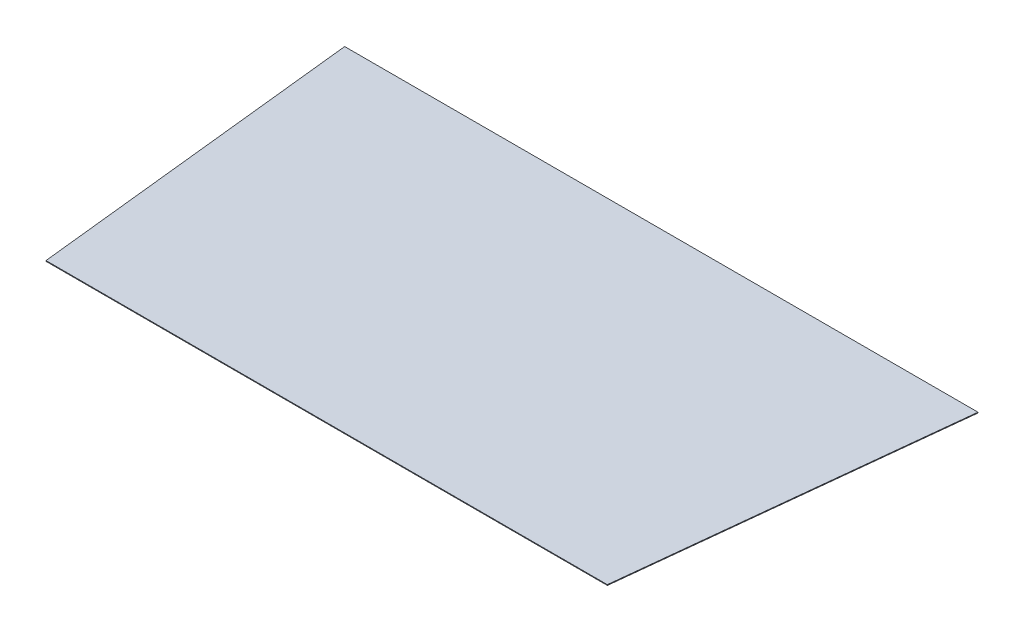
SolidWorks part; units mm, degrees
ref_plane "Front Plane" through (0, 0, 0) normal (0, 0, 1) x (1, 0, 0)
ref_plane "Top Plane" through (0, 0, 0) normal (0, 1, 0) x (1, 0, 0)
ref_plane "Right Plane" through (0, 0, 0) normal (1, 0, 0) x (0, 0, -1)
sketch "Sketch1" plane through (0, 0, 0) normal (0, 1, 0) x (1, 0, 0)
  line L0 (-292.7132, 159.1474) -> (587.2868, 159.1474)
  line L1 (587.2868, 159.1474) -> (537.2868, -305.8526)
  line L3 (-242.7132, -305.8526) -> (-292.7132, 159.1474)
  line L4 (-242.7132, -305.8526) -> (537.2868, -305.8526)
  dimension "D1" = 465
  dimension "D2" = 780
  dimension "D3" = 880
  dimension "D4" = 50
extrude "Boss-Extrude1" add sketch "Sketch1" along normal blind 1
